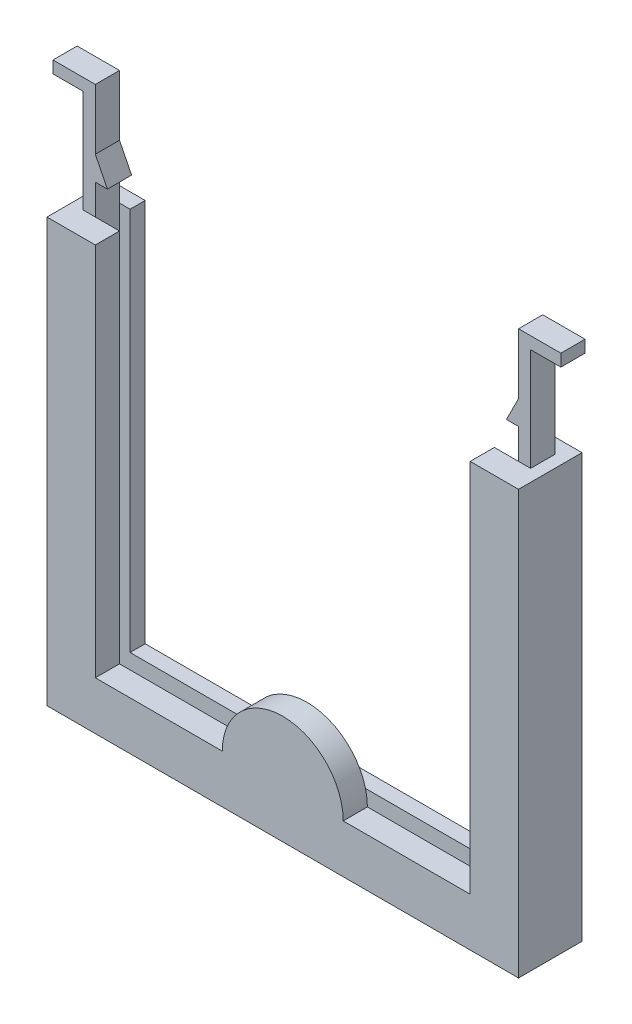
SolidWorks part; units mm, degrees
ref_plane "Plan de face" through (0, 0, 0) normal (0, 0, 1) x (1, 0, 0)
ref_plane "Plan de dessus" through (0, 0, 0) normal (0, 1, 0) x (1, 0, 0)
ref_plane "Plan de droite" through (0, 0, 0) normal (1, 0, 0) x (0, 0, -1)
sketch "Esquisse1" plane through (0, 0, 0) normal (0, 0, 1) x (1, 0, 0)
  line L0 (-74, 70) -> (-74, 4)
  line L1 (0, 0) -> (-78, 0)
  line L2 (0, 0) -> (0, 70)
  line L3 (0, 70) -> (-78, 70)
  line L4 (-78, 0) -> (-78, 70)
  line L5 (-74, 4) -> (-4, 4)
  line L6 (-4, 4) -> (-4, 70)
  dimension "D1" = 70
  dimension "D2" = 78
  dimension "D3" = 4
  dimension "D4" = 4
  dimension "D5" = 4
extrude "Boss.-Extru.1" add sketch "Esquisse1" along normal blind 6.5 contours L6 L5 L0 L3 L4 L1 L2
sketch "Esquisse2" plane through (0, 0, 0) normal (0, 0, -1) x (-1, 0, 0)
  line L0 (0, 70) -> (5.75, 70)
  line L1 (5.75, 70) -> (5.75, 6.5)
  line L2 (5.75, 6.5) -> (72.25, 6.5)
  line L3 (72.25, 6.5) -> (72.25, 70)
  line L4 (72.25, 70) -> (78, 70)
  line L5 (78, 70) -> (78, 0)
  line L6 (78, 0) -> (0, 0)
  line L7 (0, 0) -> (0, 70)
  dimension "D1" = 5.75
  dimension "D2" = 5.75
  dimension "D3" = 6.5
extrude "Boss.-Extru.2" add sketch "Esquisse2" against normal blind 2.5
sketch "Esquisse3" plane through (0, 70, 0) normal (0, 1, 0) x (1, 0, 0)
  line L0 (0, -6.5) -> (-4, -6.5) construction
  line L1 (-74, -6.5) -> (-76, -6.5)
  line L2 (-74, -6.5) -> (-74, -2.5)
  line L3 (-74, -2.5) -> (-76, -2.5)
  line L4 (-76, -6.5) -> (-76, -2.5)
  line L5 (-4, -6.5) -> (-2, -6.5)
  line L6 (-4, -6.5) -> (-4, -2.5)
  line L7 (-4, -2.5) -> (-2, -2.5)
  line L8 (-2, -6.5) -> (-2, -2.5)
  dimension "D1" = 2
  dimension "D2" = 2
extrude "Boss.-Extru.3" add sketch "Esquisse3" along normal blind 9
sketch "Esquisse4" plane through (0, 0, 6.5) normal (0, 0, 1) x (1, 0, 0)
  line L0 (-4, 79) -> (-6, 75)
  line L1 (-4, 4) -> (-4, 79) construction
  line L2 (-6, 75) -> (-4, 75)
  line L3 (-4, 75) -> (-4, 79)
  line L4 (-4, 79) -> (-2, 79) construction
  line L5 (-74, 79) -> (-72, 75)
  line L6 (-72, 75) -> (-74, 75)
  line L7 (-74, 79) -> (-74, 4) construction
  line L8 (-74, 75) -> (-74, 79)
  dimension "D1" = 4
  dimension "D2" = 0
  dimension "D3" = 2
  dimension "D4" = 4
  dimension "D5" = 2
extrude "Boss.-Extru.4" add sketch "Esquisse4" against normal up to vertex
sketch "Esquisse5" plane through (0, 0, 6.5) normal (0, 0, 1) x (1, 0, 0)
  line L0 (0, 70) -> (0, 0)
  line L1 (0, 0) -> (-78, 0)
  line L2 (-78, 0) -> (-78, 70)
  line L3 (-78, 70) -> (-70, 70)
  line L4 (-70, 70) -> (-70, 8)
  line L5 (-70, 8) -> (-8, 8)
  line L6 (-8, 8) -> (-8, 70)
  line L7 (-8, 70) -> (0, 70)
  dimension "D1" = 8
  dimension "D2" = 8
  dimension "D3" = 8
extrude "Boss.-Extru.5" add sketch "Esquisse5" along normal blind 4
sketch "Esquisse6" plane through (0, 79, 0) normal (0, 1, 0) x (1, 0, 0)
  line L1 (-2, -6.5) -> (-4, -6.5)
  line L2 (-2, -6.5) -> (-2, -2.5)
  line L3 (-2, -2.5) -> (-4, -2.5)
  line L4 (-4, -6.5) -> (-4, -2.5)
  line L5 (-74, -6.5) -> (-76, -6.5)
  line L6 (-74, -6.5) -> (-74, -2.5)
  line L7 (-74, -2.5) -> (-76, -2.5)
  line L8 (-76, -6.5) -> (-76, -2.5)
extrude "Boss.-Extru.6" add sketch "Esquisse6" along normal blind 10
sketch "Esquisse7" plane through (-2, 0, 0) normal (1, 0, 0) x (0, 0, -1)
  line L0 (-2.5, 89) -> (-2.5, 70) construction
  line L1 (-6.5, 89) -> (-2.5, 89)
  line L2 (-6.5, 89) -> (-6.5, 87)
  line L3 (-6.5, 87) -> (-2.5, 87)
  line L4 (-2.5, 89) -> (-2.5, 87)
  dimension "D1" = 2
extrude "Boss.-Extru.7" add sketch "Esquisse7" along normal blind 5
sketch "Esquisse8" plane through (-76, 0, 0) normal (-1, 0, 0) x (0, 0, 1)
  line L0 (2.5, 89) -> (2.5, 70) construction
  line L1 (6.5, 89) -> (2.5, 89)
  line L2 (6.5, 89) -> (6.5, 87)
  line L3 (6.5, 87) -> (2.5, 87)
  line L4 (2.5, 89) -> (2.5, 87)
  dimension "D1" = 2
extrude "Boss.-Extru.8" add sketch "Esquisse8" along normal blind 5
sketch "Esquisse9" plane through (0, 0, 10.5) normal (0, 0, 1) x (1, 0, 0)
  line L0 (-8, 8) -> (-70, 8) construction
  line L1 (-8, 8) -> (-29, 8)
  line L9 (0, 70) -> (-8, 70)
  line L10 (-8, 70) -> (-8, 8)
  line L11 (-8, 8) -> (-70, 8)
  line L12 (-70, 8) -> (-70, 70)
  line L13 (-70, 70) -> (-78, 70)
  line L14 (-78, 70) -> (-78, 0)
  line L15 (-78, 0) -> (0, 0)
  line L16 (0, 0) -> (0, 70)
  line L17 (0, 70) -> (-8, 70)
  line L18 (-8, 70) -> (-8, 8)
  line L19 (-49, 8) -> (-70, 8)
  line L20 (-70, 8) -> (-70, 70)
  line L21 (-70, 70) -> (-78, 70)
  line L22 (-78, 70) -> (-78, 0)
  line L23 (-78, 0) -> (0, 0)
  line L24 (0, 0) -> (0, 70)
  arc A0 (-49, 8) -> (-29, 8) centre (-39, 8) cw
  dimension "D1" = 10
  dimension "D2" = 0
extrude "Boss.-Extru.9" add sketch "Esquisse9" against normal up to vertex
